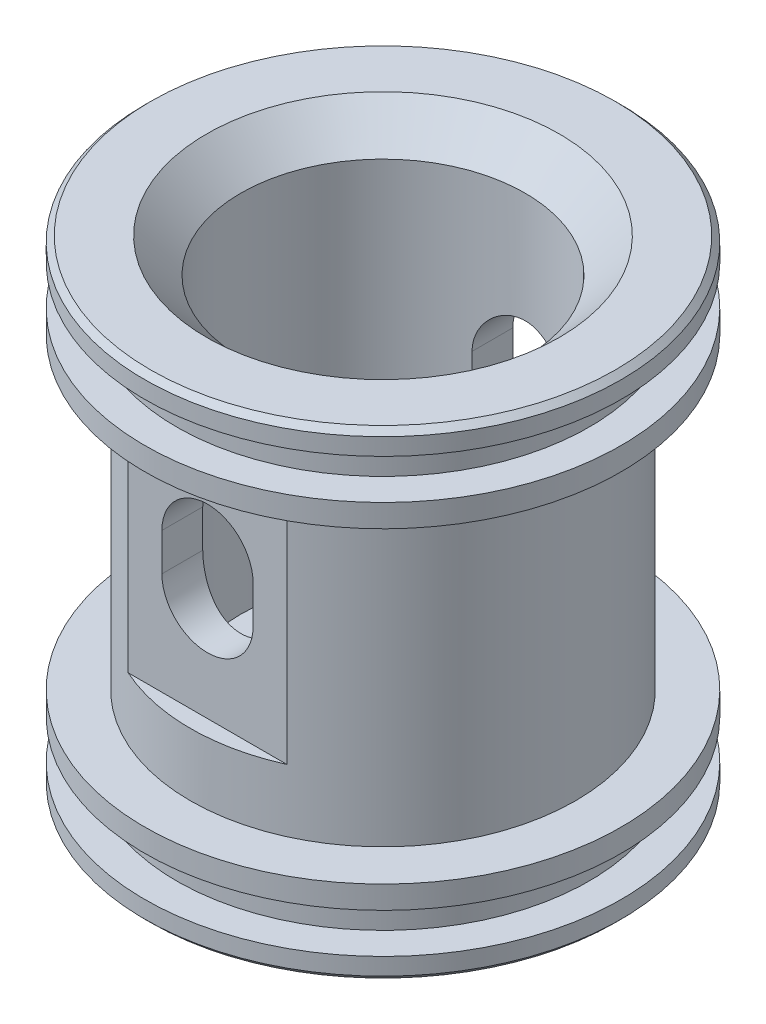
SolidWorks part; units mm, degrees
material "Brass"
ref_plane "Front Plane" through (0, 0, 0) normal (0, 0, 1) x (1, 0, 0)
ref_plane "Top Plane" through (0, 0, 0) normal (0, 1, 0) x (1, 0, 0)
ref_plane "Right Plane" through (0, 0, 0) normal (1, 0, 0) x (0, 0, -1)
sketch "Sketch1" plane through (0, 0, 0) normal (0, 0, 1) x (1, 0, 0)
  line L1 (0, 0) -> (12.475, 0)
  line L2 (0, 0) -> (0, -7)
  line L3 (0, -7) -> (20.9, -7)
  line L4 (18.1, -1.5) -> (18.1, -5)
  line L6 (16.9, 0.5) -> (16.9, 27.5)
  line L8 (12.475, 0) -> (12.475, 35)
  line L11 (12.475, 35) -> (20.9, 35)
  line L12 (20.9, 33) -> (20.9, 35)
  line L15 (16.9, 27.5) -> (20.9, 27.5)
  line L16 (20.9, 29.5) -> (20.9, 27.5)
  line L17 (16.9, 0.5) -> (20.9, 0.5)
  line L19 (18.1, -1.5) -> (20.9, -1.5)
  line L20 (20.9, 0.5) -> (20.9, -1.5)
  line L23 (18.1, -5) -> (20.9, -5)
  line L24 (20.9, -7) -> (20.9, -5)
  line L25 (18.1, 33) -> (18.1, 29.5)
  line L26 (18.1, 29.5) -> (20.9, 29.5)
  line L27 (18.1, 33) -> (20.9, 33)
  dimension "D1" = 20.9
  dimension "D2" = 3.5
  dimension "D3" = 42
  dimension "D4" = 2
  dimension "D5" = 12.475
  dimension "D6" = 4
  dimension "D7" = 18.1
  dimension "D8" = 35
revolve "Revolve1" add sketch "Sketch1" angle 360 about L2
chamfer "Chamfer1" distance 3 angle 45 1 edges at (-12.475, 35, 0)
chamfer "Chamfer2" distance 0.5 angle 45 2 edges at (-20.9, -7, 0) (-20.9, 35, 0)
sketch "Sketch2" plane through (0, -7, 0) normal (0, -1, 0) x (1, 0, 0)
  circle A0 centre (0, 0) radius 4
  dimension "D1" = 8
extrude "Cut-Extrude1" cut sketch "Sketch2" against normal through all
sketch "Sketch3" plane through (0, 0, 0) normal (1, 0, 0) x (0, 0, -1)
  line L0 (-16.9, 27.5) -> (-16.9, 0.5) construction
  line L1 (15.4, 27.5) -> (16.9, 27.5)
  line L2 (15.4, 27.5) -> (15.4, 6)
  line L3 (15.4, 6) -> (16.9, 6)
  line L4 (16.9, 27.5) -> (16.9, 6)
  line L5 (-16.9, 27.5) -> (-15.4, 27.5)
  line L6 (-16.9, 27.5) -> (-16.9, 6)
  line L7 (-16.9, 6) -> (-15.4, 6)
  line L8 (-15.4, 27.5) -> (-15.4, 6)
  line L9 (16.9, 0.5) -> (16.9, 27.5) construction
  line L10 (-16.9, 27.5) -> (16.9, 27.5) construction
  dimension "D1" = 21.5
  dimension "D2" = 1.5
extrude "Cut-Extrude2" cut sketch "Sketch3" against normal through all both and the other way through all
sketch "Sketch4" plane through (0, 0, 15.4) normal (0, 0, 1) x (1, 0, 0)
  line L0 (0, 18.3) -> (0, 15) construction
  line L1 (4, 18.3) -> (4, 15)
  line L2 (-4, 18.3) -> (-4, 15)
  line L3 (20.4, 35) -> (-20.4, 35) construction
  arc A0 (4, 18.3) -> (-4, 18.3) centre (0, 18.3) ccw
  arc A1 (-4, 15) -> (4, 15) centre (0, 15) ccw
  point P3 (0, 16.65)
  point P8 (0, 22.3)
  point P9 (0, 11)
  dimension "D1" = 8
  dimension "D2" = 11.3
  dimension "D3" = 12.7
extrude "Cut-Extrude3" cut sketch "Sketch4" against normal through all both and the other way through all
